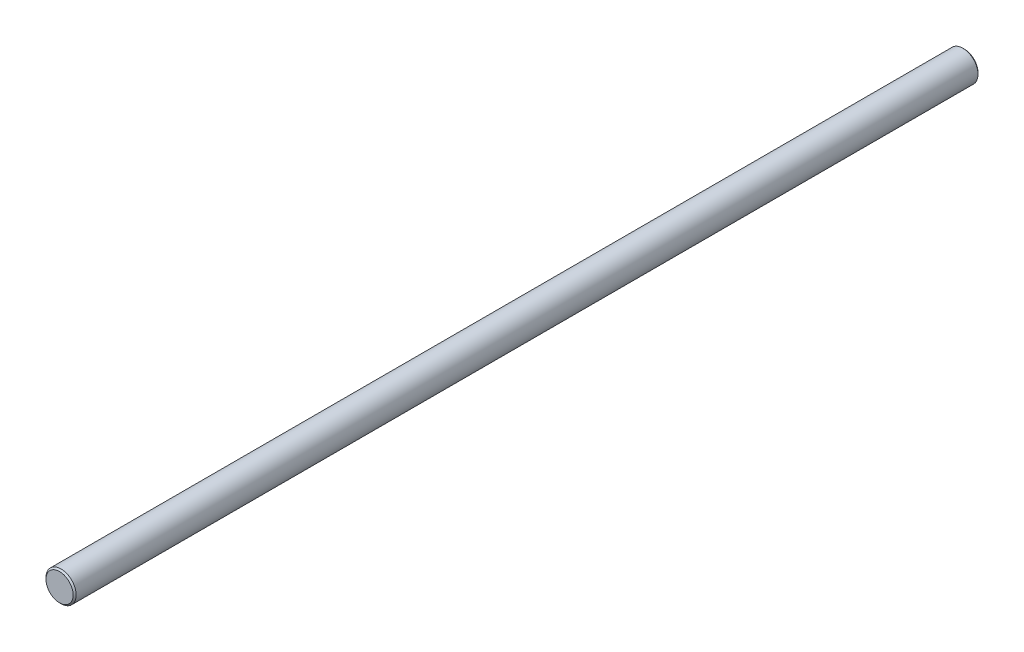
SolidWorks part; units mm, degrees
ref_plane "Plano frontal" through (0, 0, 0) normal (0, 0, 1) x (1, 0, 0)
ref_plane "Plano superior" through (0, 0, 0) normal (0, 1, 0) x (1, 0, 0)
ref_plane "Plano direito" through (0, 0, 0) normal (1, 0, 0) x (0, 0, -1)
sketch "Esboço1" plane through (0, 0, 0) normal (0, 0, 1) x (1, 0, 0)
  circle A0 centre (0, 0) radius 5
  dimension "D1" = 10
extrude "Ressalto-extrusão1" add sketch "Esboço1" along normal blind 300
chamfer "Chanfro1" distance 0.5 angle 45 2 edges at (5, 0, 300) (5, 0, 0)
